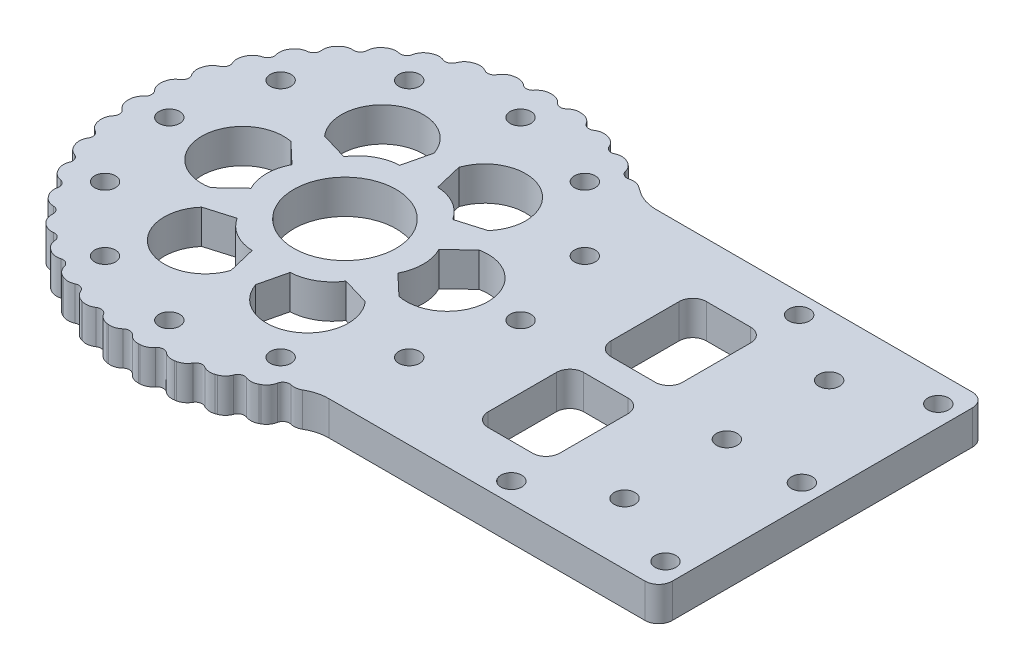
SolidWorks part; units mm, degrees
material "Thornel Mat VMA"
ref_plane "前视基准面" through (0, 0, 0) normal (0, 0, 1) x (1, 0, 0)
ref_plane "上视基准面" through (0, 0, 0) normal (0, 1, 0) x (1, 0, 0)
ref_plane "右视基准面" through (0, 0, 0) normal (1, 0, 0) x (0, 0, -1)
other "Configuration Table"
sketch "草图1" plane through (0, 0, 0) normal (0, 1, 0) x (1, 0, 0)
  line L1 (-105, -24) -> (105, -24)
  line L2 (-105, -24) -> (-105, 24) construction
  line L3 (-105, 24) -> (105, 24)
  line L4 (105, -24) -> (105, 24)
  line L5 (-105, -24) -> (105, 24) construction
  line L6 (-105, 24) -> (105, -24) construction
  circle A0 centre (105, 0) radius 24
  circle A1 centre (-105, 0) radius 37
  point P0 (0, 0)
  dimension "D1" = 48
  dimension "D3" = 74
  dimension "D2" = 210
extrude "凸台-拉伸1" add sketch "草图1" along normal blind 5
fillet "圆角2" radius 40 2 edges at (-76.8397, 2.5, -24) (-76.8397, 2.5, 24)
sketch "草图2" plane through (0, 0, 0) normal (0, -1, 0) x (1, 0, 0)
  line L0 (118.435, 13.435) -> (105, 0) construction
  line L1 (105, 0) -> (129, 0) construction
  circle A0 centre (105, 0) radius 19 construction
  circle A1 centre (118.435, 13.435) radius 1.275
  arc A2 (105, -24) -> (105, 24) centre (105, 0) ccw construction
  circle A3 centre (118.435, -13.435) radius 1.275
  circle A4 centre (91.565, -13.435) radius 1.275
  circle A5 centre (91.565, 13.435) radius 1.275
  point P18 (105, 0)
  dimension "D1" = 38
  dimension "D3" = 2.55
  dimension "D4" = 4
  dimension "D2" = 45
sketch "草图3" plane through (0, 5, 0) normal (0, 1, 0) x (1, 0, 0)
  circle A0 centre (-105, 0) radius 17.25 construction
  circle A1 centre (-122.25, 0) radius 2.025
  circle A2 centre (-113.625, 14.9389) radius 2.025
  circle A3 centre (-96.375, 14.9389) radius 2.025
  circle A4 centre (-87.75, 0) radius 2.025
  circle A5 centre (-96.375, -14.9389) radius 2.025
  circle A6 centre (-113.625, -14.9389) radius 2.025
  point P17 (-105, 0)
  dimension "D1" = 34.5
  dimension "D2" = 4.05
  dimension "D3" = 6
sketch "草图5" plane through (0, 5, 0) normal (0, 1, 0) x (1, 0, 0)
  circle A0 centre (-105, 0) radius 22.5
  dimension "D1" = 45
extrude "切除-拉伸3" cut sketch "草图5" against normal through all
sketch "草图6" plane through (0, 5, 0) normal (0, 1, 0) x (1, 0, 0)
  circle A0 centre (-105, 0) radius 30 construction
  circle A1 centre (-135, 0) radius 1.525
  circle A2 centre (-120, 25.9808) radius 1.525
  circle A3 centre (-90, 25.9808) radius 1.525
  circle A4 centre (-75, 0) radius 1.525
  circle A5 centre (-90, -25.9808) radius 1.525
  circle A6 centre (-120, -25.9808) radius 1.525
  point P17 (-105, 0)
  dimension "D1" = 60
  dimension "D2" = 3.05
  dimension "D3" = 6
extrude "切除-拉伸4" cut sketch "草图6" against normal through all
sketch "草图7" plane through (0, 5, 0) normal (0, 1, 0) x (1, 0, 0)
  line L0 (-62.1865, 24) -> (105, 24) construction
  line L1 (0, 0) -> (50000, 0) construction
  circle A0 centre (-60, 18.25) radius 1.525
  circle A1 centre (-27, 18.25) radius 1.525
  circle A2 centre (6, 18.25) radius 1.525
  circle A3 centre (39, 18.25) radius 1.525
  circle A4 centre (72, 18.25) radius 1.525
  circle A5 centre (72, -18.25) radius 1.525
  circle A6 centre (39, -18.25) radius 1.525
  circle A7 centre (6, -18.25) radius 1.525
  circle A8 centre (-27, -18.25) radius 1.525
  circle A9 centre (-60, -18.25) radius 1.525
  dimension "D1" = 3.05
  dimension "D2" = 5.75
  dimension "D3" = 60
  dimension "D5" = 33
  dimension "D4" = 5
sketch "草图8" plane through (0, 5, 0) normal (0, 1, 0) x (1, 0, 0)
  line L0 (118.435, -13.435) -> (105, 0) construction
  circle A0 centre (105, 0) radius 18.5
  dimension "D1" = 37
extrude "切除-拉伸6" cut sketch "草图8" against normal through all
sketch "草图9" plane through (0, 5, 0) normal (0, 1, 0) x (1, 0, 0)
  circle A0 centre (105, 0) radius 25 construction
  circle A1 centre (130, 0) radius 1.275
  circle A2 centre (117.5, -21.6506) radius 1.275
  circle A3 centre (92.5, -21.6506) radius 1.275
  circle A4 centre (80, 0) radius 1.275
  circle A5 centre (92.5, 21.6506) radius 1.275
  circle A6 centre (117.5, 21.6506) radius 1.275
  point P17 (105, 0)
  dimension "D1" = 50
  dimension "D2" = 2.55
  dimension "D3" = 6
extrude "切除-拉伸7" cut sketch "草图9" against normal through all
sketch "草图10" plane through (0, 5, 0) normal (0, 1, 0) x (1, 0, 0)
  line L0 (0, 0) -> (50000, 0) construction
  line L1 (-17, -17) -> (-17, 17)
  line L2 (-51, -17) -> (-33, -17)
  line L3 (-51, -17) -> (-51, 17)
  line L4 (-51, 17) -> (-33, 17)
  line L5 (-33, -17) -> (-33, 17)
  line L6 (-51, -17) -> (-33, 17) construction
  line L7 (-51, 17) -> (-33, -17) construction
  line L8 (-17, -17) -> (1, -17)
  line L9 (1, -17) -> (1, 17)
  line L10 (-17, 17) -> (1, 17)
  line L11 (17, -17) -> (17, 17)
  line L12 (17, -17) -> (35, -17)
  line L13 (35, -17) -> (35, 17)
  line L14 (17, 17) -> (35, 17)
  line L15 (51, -17) -> (51, 17)
  line L16 (51, -17) -> (69, -17)
  line L17 (69, -17) -> (69, 17)
  line L18 (51, 17) -> (69, 17)
  line L19 (-51, 11.6568) -> (-35.8287, -17)
  line L20 (-48.1713, 17) -> (-33, -11.6568)
  point P3 (-42, 0)
  dimension "D1" = 34
  dimension "D2" = 18
  dimension "D3" = 42
  dimension "D5" = 25
  dimension "D6" = 5
  dimension "D4" = 4
sketch "草图11" plane through (0, 5, 0) normal (0, 1, 0) x (1, 0, 0)
  circle A0 centre (-105.0002, -0.0002) radius 42.5
  dimension "D1" = 85
extrude "凸台-拉伸2" add sketch "草图11" against normal up to surface (5 mm away) up to face at (92.5, 0, -20.3756)
fillet "圆角4" radius 20 2 edges at (-70.5461, 2.5, 24.8833) (-70.5465, 2.5, -24.8834)
sketch "草图13" plane through (0, 5, 0) normal (0, 1, 0) x (1, 0, 0)
  circle A0 centre (-105.0002, -0.0002) radius 31
  dimension "D1" = 62
extrude "切除-拉伸10" cut sketch "草图13" against normal up to surface (5 mm away) up to face at (92.5, 0, -20.3756)
sketch "草图12" plane through (0, 5, 0) normal (0, 1, 0) x (1, 0, 0)
  circle A0 centre (-105.0002, -0.0002) radius 36.75 construction
  circle A1 centre (-105.0002, 36.7498) radius 1.525
  circle A2 centre (-79.014, 25.986) radius 1.525
  circle A3 centre (-68.2502, -0.0002) radius 1.525
  circle A4 centre (-79.014, -25.9864) radius 1.525
  circle A5 centre (-105.0002, -36.7502) radius 1.525
  circle A6 centre (-130.9863, -25.9864) radius 1.525
  circle A7 centre (-141.7502, -0.0002) radius 1.525
  circle A8 centre (-130.9863, 25.986) radius 1.525
  arc A9 (-74.8168, 29.9199) -> (-74.8165, -29.9201) centre (-105.0002, -0.0002) ccw construction
  point P21 (-105.0002, -0.0002)
  dimension "D1" = 5.75
  dimension "D2" = 3.05
  dimension "D3" = 8
sketch "草图14" plane through (0, 5, 0) normal (0, 1, 0) x (1, 0, 0)
  circle A0 centre (104.9998, -0.0002) radius 37.5
  dimension "D1" = 75
extrude "凸台-拉伸3" add sketch "草图14" against normal up to surface (5 mm away) up to face at (-105.0002, 0, 31.0002)
sketch "草图15" plane through (0, 5, 0) normal (0, 1, 0) x (1, 0, 0)
  circle A0 centre (104.9998, -0.0002) radius 28.5
  arc A1 (76.1856, -24) -> (76.186, 24) centre (104.9998, -0.0002) ccw construction
  dimension "D1" = 57
extrude "切除-拉伸11" cut sketch "草图15" against normal up to surface (5 mm away) up to face at (-105.0002, 0, 31.0002)
sketch "草图16" plane through (0, 5, 0) normal (0, 1, 0) x (1, 0, 0)
  circle A14 centre (104.9998, -0.0002) radius 33 construction
  circle A15 centre (137.9998, -0.0002) radius 2.025
  circle A16 centre (121.4998, -28.579) radius 2.025
  circle A17 centre (88.4998, -28.579) radius 2.025
  circle A18 centre (71.9998, -0.0002) radius 2.025
  circle A19 centre (88.4998, 28.5786) radius 2.025
  circle A20 centre (121.4998, 28.5786) radius 2.025
  point P16 (104.9998, -0.0002)
  dimension "D1" = 66
  dimension "D2" = 4.05
  dimension "D3" = 6
extrude "切除-拉伸12" cut sketch "草图16" against normal up to surface (5 mm away) up to face at (104.9998, 0, 28.5002)
fillet "圆角5" radius 20 2 edges at (76.1856, 2.5, 24) (76.186, 2.5, -24)
sketch "草图17" plane through (0, 5, 0) normal (0, 1, 0) x (1, 0, 0)
  circle A0 centre (-105.0002, -0.0002) radius 31
  dimension "D1" = 62
extrude "凸台-拉伸4" add sketch "草图17" against normal up to surface (5 mm away) up to face at (137.9998, 0, 2.0252)
sketch "草图18" plane through (0, 5, 0) normal (0, 1, 0) x (1, 0, 0)
  line L0 (-103.1913, 14.8903) -> (-102.2151, 10.8237)
  line L1 (-93.009, 9.0116) -> (-97.0189, 7.8237)
  line L2 (-105.0002, -0.0002) -> (-86.4386, 18.5613) construction
  line L3 (-97.5002, 12.9902) -> (-105.0002, -0.0002) construction
  line L4 (-105.0002, -0.0002) -> (-102.5002, 4.3299) construction
  line L5 (-105.0002, -0.0002) -> (-90.0002, -0.0002) construction
  line L6 (-102.2151, 10.8237) -> (-97.0189, 7.8237) construction
  circle A0 centre (-131.2502, -0.0002) radius 2.025 construction
  circle A1 centre (-86.4386, 18.5613) radius 2.025 construction
  circle A2 centre (-123.5617, 18.5613) radius 2.025 construction
  circle A3 centre (-105.0002, 26.2498) radius 2.025 construction
  circle A4 centre (-131.2502, -0.0002) radius 2.025 construction
  circle A5 centre (-86.4386, 18.5613) radius 2.025 construction
  circle A6 centre (-123.5617, 18.5613) radius 2.025 construction
  circle A7 centre (-105.0002, 26.2498) radius 2.025 construction
  circle A8 centre (-105.0002, -0.0002) radius 15 construction
  arc A9 (-103.1913, 14.8903) -> (-93.009, 9.0116) centre (-97.5002, 12.9902) cw
  circle A10 centre (-86.4386, 18.5613) radius 4 construction
  circle A11 centre (-105.0002, 26.2498) radius 4 construction
  arc A12 (-102.2151, 10.8237) -> (-97.0189, 7.8237) centre (-102.5002, 4.3299) cw
  dimension "D1" = 8
  dimension "D2" = 8
  dimension "D4" = 6
  dimension "D6" = 6.5
  dimension "D3" = 30
  dimension "D5" = 5
  dimension "D8" = 6
  dimension "D9" = 60
extrude "切除-拉伸13" cut sketch "草图18" against normal blind 10
pattern_circular "阵列(圆周)1" count 6 over 360 about axis through (-105.0002, 0, 0.0002) along (0, 1, 0) of "切除-拉伸13"
sketch "草图19" plane through (0, 5, 0) normal (0, 1, 0) x (1, 0, 0)
  circle A0 centre (-105.0002, -0.0002) radius 7.5
  dimension "D1" = 15
extrude "切除-拉伸14" cut sketch "草图19" against normal blind 10
sketch "草图20" plane through (0, 5, 0) normal (0, 1, 0) x (1, 0, 0)
  line L0 (0, 0) -> (170.8247, 0) construction
  line L1 (-35.0002, 63.4711) -> (170.8247, 63.4711)
  line L2 (-35.0002, 63.4711) -> (-35.0002, -63.4711)
  line L3 (-35.0002, -63.4711) -> (170.8247, -63.4711)
  line L4 (170.8247, 63.4711) -> (170.8247, -63.4711)
  circle A0 centre (-105.0002, -0.0002) radius 7.5 construction
  dimension "D1" = 126.9423
  dimension "D2" = 205.8249
  dimension "D3" = 70
extrude "切除-拉伸15" cut sketch "草图20" against normal through all
sketch "草图21" plane through (0, 5, 0) normal (0, 1, 0) x (1, 0, 0)
  line L0 (-35.0002, 24) -> (-85.379, 24)
  line L1 (-35.0002, -24) -> (-85.3785, -24)
  line L5 (-35.0002, -24) -> (-35.0002, 24)
  line L6 (-35.0002, 24) -> (-60.6129, 24)
  line L7 (-60.6125, -24) -> (-35.0002, -24)
  line L8 (-35.0002, -24) -> (-35.0002, 24)
  line L9 (-35.0002, 24) -> (-60.6129, 24)
  line L10 (-60.6125, -24) -> (-35.0002, -24)
  circle A0 centre (-105.0002, -0.0002) radius 31
  arc A4 (-74.8168, 29.9199) -> (-60.6129, 24) centre (-60.6129, 44) ccw
  arc A5 (-74.8168, 29.9199) -> (-74.8165, -29.9201) centre (-105.0002, -0.0002) ccw
  arc A6 (-60.6125, -24) -> (-74.8165, -29.9201) centre (-60.6125, -44) ccw
  arc A7 (-74.8168, 29.9199) -> (-60.6129, 24) centre (-60.6129, 44) ccw
  arc A8 (-74.8168, 29.9199) -> (-74.8165, -29.9201) centre (-105.0002, -0.0002) ccw
  arc A9 (-60.6125, -24) -> (-74.8165, -29.9201) centre (-60.6125, -44) ccw
  arc M4 (-60.6129, 24) -> (-74.8168, 29.9199) centre (-60.6129, 44) cw
  arc M5 (-74.8168, 29.9199) -> (-74.8165, -29.9201) centre (-105.0002, -0.0002) ccw
  arc M6 (-74.8165, -29.9201) -> (-60.6125, -24) centre (-60.6125, -44) cw
  dimension "D1" = 62
  dimension "D2" = 0
extrude "切除-拉伸16" cut sketch "草图21" against normal through all contours A0 L0 L1 M4 M5 M6
sketch "草图23" plane through (0, 5, 0) normal (0, 1, 0) x (1, 0, 0)
  line L0 (-38.0002, 0) -> (0, 0) construction
  line L1 (-35.0002, 24) -> (-35.0002, -24) construction
  circle A0 centre (-38.0002, 0) radius 1.525
  circle A1 centre (-38.0002, 20) radius 1.525
  circle A2 centre (-38.0002, -20) radius 1.525
  dimension "D1" = 3.05
  dimension "D2" = 3
  dimension "D3" = 20
extrude "切除-拉伸17" cut sketch "草图23" against normal through all
sketch "草图26" plane through (0, 5, 0) normal (0, 1, 0) x (1, 0, 0)
  circle A0 centre (-105.0002, -0.0002) radius 25.75 construction
  circle A1 centre (-130.7502, -0.0002) radius 1.525
  circle A2 centre (-127.3003, 12.8748) radius 1.525
  circle A3 centre (-117.8752, 22.2999) radius 1.525
  circle A4 centre (-105.0002, 25.7498) radius 1.525
  circle A5 centre (-92.1252, 22.2999) radius 1.525
  circle A6 centre (-82.7, 12.8748) radius 1.525
  circle A7 centre (-79.2502, -0.0002) radius 1.525
  circle A8 centre (-82.7, -12.8752) radius 1.525
  circle A9 centre (-92.1252, -22.3004) radius 1.525
  circle A10 centre (-105.0002, -25.7502) radius 1.525
  circle A11 centre (-117.8752, -22.3004) radius 1.525
  circle A12 centre (-127.3003, -12.8752) radius 1.525
  point P17 (-105.0002, -0.0002)
  dimension "D1" = 51.5
  dimension "D2" = 3.05
  dimension "D3" = 12
extrude "切除-拉伸18" cut sketch "草图26" against normal through all
sketch "草图27" plane through (0, 5, 0) normal (0, 1, 0) x (1, 0, 0)
  line L0 (0, 0) -> (-50000, 0) construction
  line L1 (-35.0002, 24) -> (-35.0002, -24) construction
  line L3 (-70.0002, -16) -> (-45.0002, -16)
  line L4 (-70.0002, -16) -> (-70.0002, 16)
  line L5 (-70.0002, 16) -> (-45.0002, 16)
  line L6 (-45.0002, -16) -> (-45.0002, 16)
  line L7 (-70.0002, -16) -> (-45.0002, 16) construction
  line L8 (-70.0002, 16) -> (-45.0002, -16) construction
  line L9 (0, 2) -> (-50000, 2)
  line L10 (0, -2) -> (-50000, -2)
  line L11 (-57.5002, 16) -> (-57.5002, -16)
  line L12 (-59.5002, 16) -> (-59.5002, -16)
  line L13 (-55.5002, 16) -> (-55.5002, -16)
  point P3 (-57.5002, 0)
  dimension "D1" = 32
  dimension "D2" = 25
  dimension "D3" = 10
  dimension "D4" = 2
  dimension "D5" = 2
  dimension "D6" = 2
  dimension "D7" = 2
extrude "切除-拉伸19" cut sketch "草图27" against normal through all contours L12 L10 L4 L3 | L12 L5 L4 L9
fillet "圆角6" radius 2 4 edges at (-59.5002, 2.5, -2) (-70.0002, 2.5, -2) (-59.5002, 2.5, -16) (-70.0002, 2.5, -16)
fillet "圆角8" radius 2 4 edges at (-59.5002, 2.5, 16) (-70.0002, 2.5, 16) (-59.5002, 2.5, 2) (-70.0002, 2.5, 2)
fillet "圆角10" radius 2 2 edges at (-35.0002, 2.5, -24) (-35.0002, 2.5, 24)
fillet "圆角11" radius 6 2 edges at (-85.3785, 2.5, 24) (-85.379, 2.5, -24)
sketch "草图28" plane through (0, 5, 0) normal (0, 1, 0) x (1, 0, 0)
  line L0 (-105.0002, 25.7498) -> (-105.0002, -0.0002) construction
  line L1 (-105.0002, -0.0002) -> (-113.0235, 29.9435) construction
  circle A0 centre (-113.0235, 29.9435) radius 1
  arc A1 (-86.8558, 25.1351) -> (-86.8554, -25.1352) centre (-105.0002, -0.0002) ccw construction
  dimension "D2" = 2
  dimension "D1" = 15
extrude "切除-拉伸20" cut sketch "草图28" against normal through all
pattern_circular "阵列(圆周)2" count 40 over 360 about axis through (-105.0002, 0, 0.0002) along (0, 1, 0) skipping 23, 24, 25, 26, 27, 28, 29, 30, 31, 32, 33, 34 of "切除-拉伸20"
fillet "圆角12" radius 2 56 edges at (-105.6232, 2.5, 30.9939) (-107.6202, 2.5, 30.8893) (-110.464, 2.5, 30.5149) (-112.4201, 2.5, 30.0991) (-115.1703, 2.5, 29.2845) (-117.0372, 2.5, 28.5678) (-119.6262, 2.5, 27.333) (-121.358, 2.5, 26.3331) (-123.7219, 2.5, 24.7084) (-125.276, 2.5, 23.45) (-127.3566, 2.5, 21.4755) (-128.6947, 2.5, 19.9894) (-130.4408, 2.5, 17.7138) (-131.53, 2.5, 16.0367) (-132.8986, 2.5, 13.5159) (-133.712, 2.5, 11.6891) (-134.6695, 2.5, 8.9852) (-135.1871, 2.5, 7.0536) (-135.7098, 2.5, 4.2333) (-135.9188, 2.5, 2.2445) (-135.9939, 2.5, -0.6229) (-135.8892, 2.5, -2.6199) (-135.5148, 2.5, -5.4637) (-135.0991, 2.5, -7.4197) (-134.2844, 2.5, -10.17) (-133.5678, 2.5, -12.0369) (-132.3329, 2.5, -14.6258) (-131.333, 2.5, -16.3576) (-129.7084, 2.5, -18.7215) (-128.4499, 2.5, -20.2756) (-126.4755, 2.5, -22.3563) (-124.9894, 2.5, -23.6943) (-122.7137, 2.5, -25.4405) (-121.0366, 2.5, -26.5296) (-118.5159, 2.5, -27.8983) (-116.689, 2.5, -28.7117) (-113.9852, 2.5, -29.6691) (-112.0536, 2.5, -30.1867) (-109.2332, 2.5, -30.7094) (-107.2445, 2.5, -30.9184) (-104.3771, 2.5, -30.9935) (-102.3801, 2.5, -30.8889) (-99.5363, 2.5, -30.5145) (-97.5802, 2.5, -30.0987) (-94.83, 2.5, -29.284) (-92.9631, 2.5, -28.5674) (-90.3741, 2.5, -27.3325) (-88.6423, 2.5, -26.3327) (-87.2866, 2.5, 25.4409) (-88.9637, 2.5, 26.53) (-91.4845, 2.5, 27.8987) (-93.3113, 2.5, 28.7121) (-96.0151, 2.5, 29.6695) (-97.9467, 2.5, 30.1871) (-100.7671, 2.5, 30.7098) (-102.7559, 2.5, 30.9189)
sketch "草图29" plane through (0, 5, 0) normal (0, 1, 0) x (1, 0, 0)
  line L0 (-59.5002, 21.7888) -> (-59.5002, 50021.7888) construction
  line L3 (-83.344, 24) -> (-37.0002, 24) construction
  line L4 (-38.0002, 0) -> (-50038.0002, 0) construction
  circle A0 centre (-59.5002, 21.1) radius 1.525
  circle A1 centre (-59.5002, -21.1) radius 1.525
  circle A2 centre (-105.0002, -0.0002) radius 7.5 construction
  dimension "D2" = 3.05
  dimension "D1" = 45.5
  dimension "D3" = 2.9
extrude "切除-拉伸21" cut sketch "草图29" against normal through all
sketch "草图30" plane through (0, 0, 0) normal (0, -1, 0) x (1, 0, 0)
  line L0 (-49.0002, 24) -> (-49.0002, 50024) construction
  line L2 (-47.0002, 0) -> (49952.9998, 0) construction
  circle A0 centre (-105.0002, 0.0002) radius 7.5 construction
  circle A1 centre (-49.0002, 0) radius 1.525
  circle A2 centre (-49.0002, 15) radius 1.525
  circle A3 centre (-49.0002, -15) radius 1.525
  dimension "D2" = 3.05
  dimension "D1" = 56
  dimension "D3" = 15
extrude "切除-拉伸22" cut sketch "草图30" against normal through all
